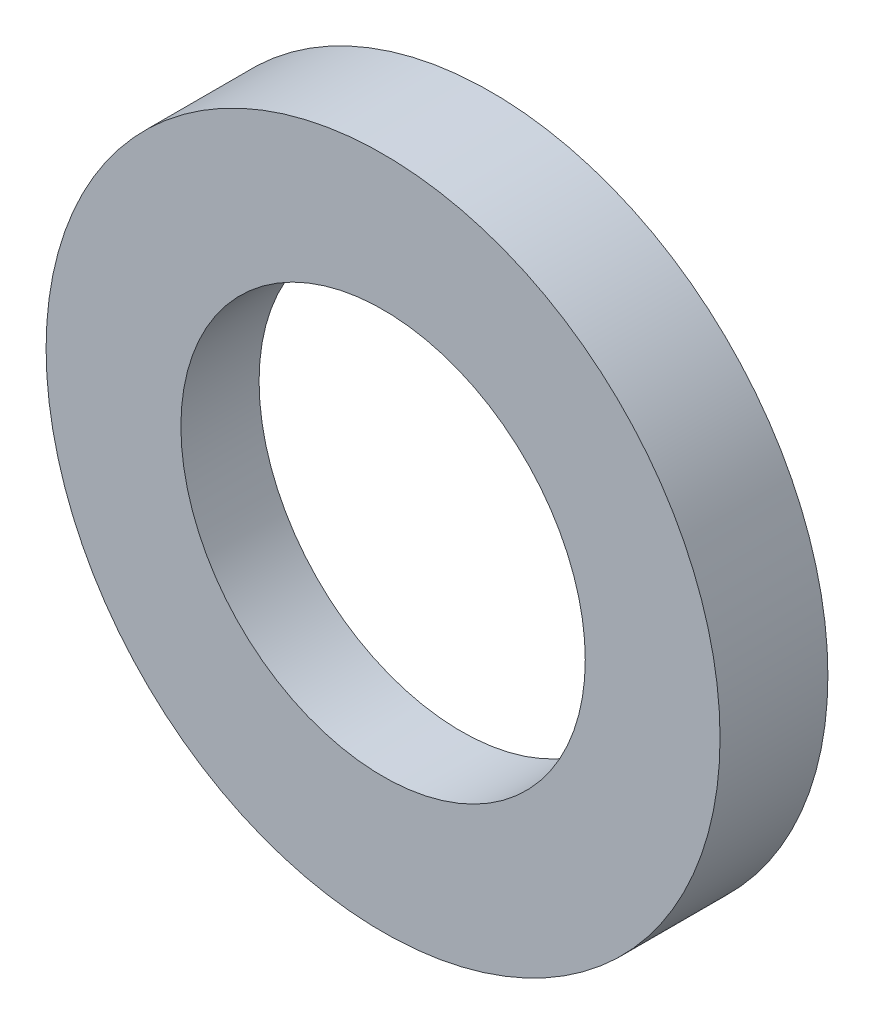
SolidWorks part; units mm, degrees
ref_plane "Front Plane" through (0, 0, 0) normal (0, 0, 1) x (1, 0, 0)
ref_plane "Top Plane" through (0, 0, 0) normal (0, 1, 0) x (1, 0, 0)
ref_plane "Right Plane" through (0, 0, 0) normal (1, 0, 0) x (0, 0, -1)
sketch "Sketch1" plane through (0, 0, 0) normal (0, 0, 1) x (1, 0, 0)
  circle A0 centre (0, 0) radius 19.05
  circle A1 centre (0, 0) radius 31.75
  dimension "D1" = 38.1
  dimension "D2" = 63.5
extrude "Boss-Extrude1" add sketch "Sketch1" along normal blind 10.16
sketch "Sketch2" plane through (0, 0, 0) normal (0, 0, -1) x (-1, 0, 0)
  circle A1 centre (0, 0) radius 25.4
  circle A2 centre (0, 0) radius 19.05
  dimension "D1" = 50.8
  dimension "D2" = 38.1
extrude "Cut-Extrude1" cut sketch "Sketch2" against normal blind 2.794
